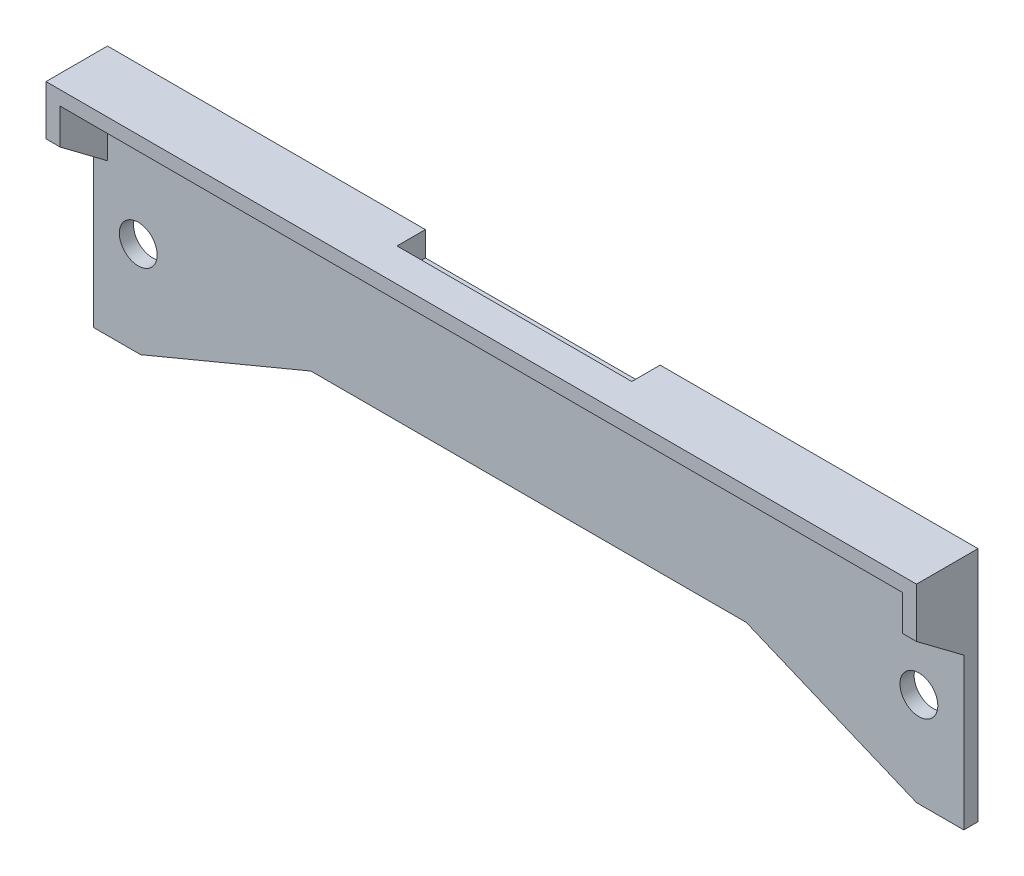
SolidWorks part; units mm, degrees
ref_plane "Front Plane" through (0, 0, 0) normal (0, 0, 1) x (1, 0, 0)
ref_plane "Top Plane" through (0, 0, 0) normal (0, 1, 0) x (1, 0, 0)
ref_plane "Right Plane" through (0, 0, 0) normal (1, 0, 0) x (0, 0, -1)
sketch "Sketch1" plane through (0, 0, 0) normal (0, 0, 1) x (1, 0, 0)
  line L0 (0, 20) -> (184, 20) construction
  line L1 (0, 0) -> (184, 0)
  line L2 (0, 0) -> (0, 50)
  line L3 (0, 50) -> (184, 50)
  line L4 (184, 0) -> (184, 50)
  line L5 (92, 50) -> (92, 0) construction
  circle A0 centre (9.5, 20) radius 4
  circle A1 centre (174.5, 20) radius 4
  dimension "D4" = 8
  dimension "D5" = 165
  dimension "D1" = 50
  dimension "D2" = 184
  dimension "D3" = 30
extrude "Boss-Extrude2" add sketch "Sketch1" along normal blind 3
sketch "Sketch2" plane through (0, 0, 3) normal (0, 0, 1) x (1, 0, 0)
  line L0 (184, 0) -> (184, 50) construction
  line L1 (0, 50) -> (184, 50)
  line L2 (0, 50) -> (0, 47)
  line L3 (0, 47) -> (184, 47)
  line L4 (184, 50) -> (184, 47)
  dimension "D1" = 3
extrude "Boss-Extrude3" add sketch "Sketch2" along normal blind 20
sketch "Sketch3" plane through (0, 0, 0) normal (-1, 0, 0) x (0, 0, 1)
  line L0 (23, 47) -> (3, 47)
  line L1 (3, 47) -> (3, 32)
  line L2 (3, 47) -> (3, 0) construction
  line L3 (3, 32) -> (23, 47)
  dimension "D1" = 15
extrude "Boss-Extrude4" add sketch "Sketch3" against normal blind 3
sketch "Sketch4" plane through (184, 0, 0) normal (1, 0, 0) x (0, 0, -1)
  line L0 (-23, 47) -> (-3, 32)
  line L1 (-3, 0) -> (-3, 47) construction
  line L2 (-3, 32) -> (-3, 47)
  line L3 (-3, 47) -> (-23, 47)
  dimension "D1" = 15
extrude "Boss-Extrude5" add sketch "Sketch4" against normal blind 3
sketch "Sketch5" plane through (0, 0, 0) normal (0, 0, -1) x (-1, 0, 0)
  line L0 (-184, 50) -> (0, 50) construction
  line L1 (-67.1888, 55.1934) -> (-116.8112, 55.1934)
  line L2 (-67.1888, 55.1934) -> (-67.1888, 44.8066)
  line L3 (-67.1888, 44.8066) -> (-116.8112, 44.8066)
  line L4 (-116.8112, 55.1934) -> (-116.8112, 44.8066)
  line L5 (-67.1888, 55.1934) -> (-116.8112, 44.8066) construction
  line L6 (-67.1888, 44.8066) -> (-116.8112, 55.1934) construction
  point P0 (-92, 50)
extrude "Cut-Extrude3" cut sketch "Sketch5" against normal blind 6
sketch "Sketch7" plane through (0, 50, 0) normal (0, 1, 0) x (1, 0, 0)
  line L0 (0, -23) -> (0, 0) construction
  line L1 (184, -23) -> (0, -23)
  line L2 (184, -23) -> (184, -13)
  line L3 (184, -13) -> (0, -13)
  line L4 (0, -23) -> (0, -13)
  dimension "D1" = 10
extrude "Cut-Extrude5" cut sketch "Sketch7" against normal blind 16
sketch "Sketch8" plane through (0, 0, 3) normal (0, 0, 1) x (1, 0, 0)
  line L0 (92, 15) -> (92, 44.8066) construction
  line L2 (116.8112, 44.8066) -> (67.1888, 44.8066) construction
  line L3 (0, 0) -> (184, 0)
  line L5 (138, 15) -> (46, 15)
  line L8 (46, 15) -> (10, 0)
  line L9 (138, 15) -> (174, 0)
  line L10 (10, 0) -> (174, 0)
  dimension "D1" = 92
  dimension "D2" = 15
  dimension "D3" = 10
extrude "Cut-Extrude7" cut sketch "Sketch8" against normal blind 16 contours L9 L5 L8 L3
